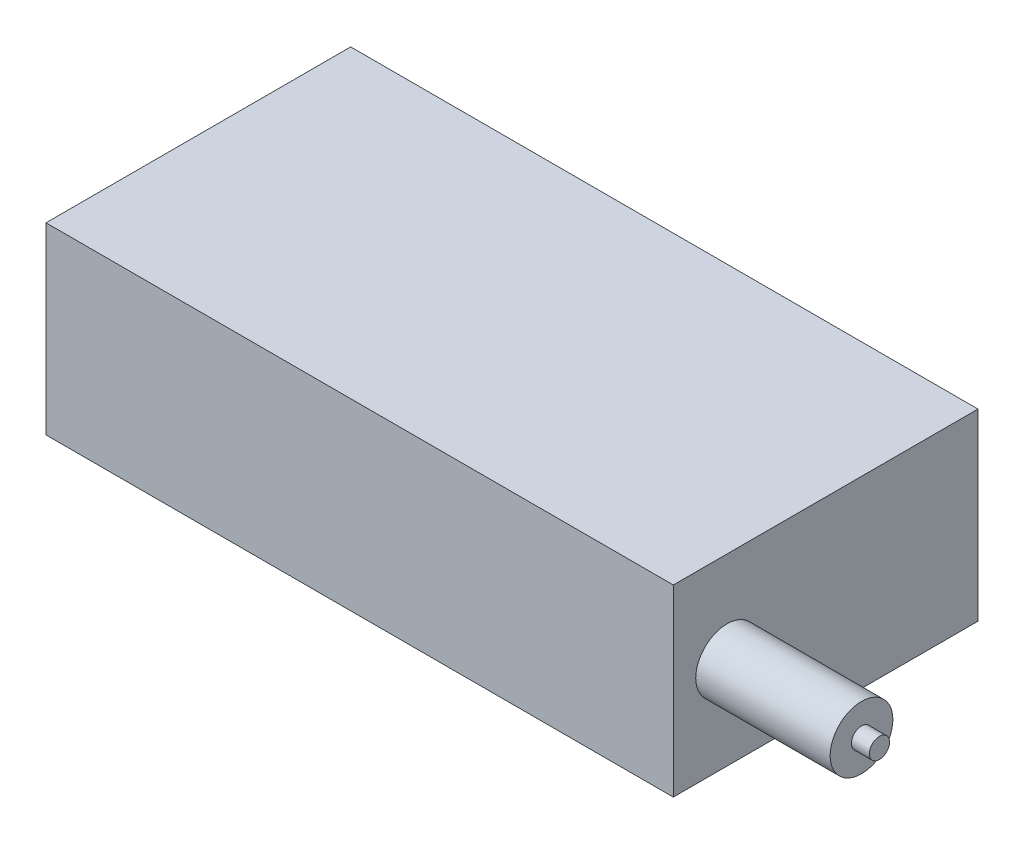
SolidWorks part; units mm, degrees
ref_plane "Front Plane" through (0, 0, 0) normal (0, 0, 1) x (1, 0, 0)
ref_plane "Top Plane" through (0, 0, 0) normal (0, 1, 0) x (1, 0, 0)
ref_plane "Right Plane" through (0, 0, 0) normal (1, 0, 0) x (0, 0, -1)
sketch "Sketch1" plane through (0, 0, 0) normal (0, 1, 0) x (1, 0, 0)
  line L1 (0, 0) -> (111.125, 0)
  line L2 (0, 0) -> (0, 53.975)
  line L3 (0, 53.975) -> (111.125, 53.975)
  line L4 (111.125, 0) -> (111.125, 53.975)
  dimension "D1" = 111.125
  dimension "D2" = 53.975
extrude "Boss-Extrude1" add sketch "Sketch1" along normal blind 32.5437
sketch "Sketch2" plane through (0, 0, 0) normal (-1, 0, 0) x (0, 0, 1)
  line L1 (-18.2562, 6.35) -> (-46.0375, 6.35)
  line L2 (-18.2562, 6.35) -> (-18.2562, 25.4)
  line L3 (-18.2562, 25.4) -> (-46.0375, 25.4)
  line L4 (-46.0375, 6.35) -> (-46.0375, 25.4)
  line L9 (-53.975, 0) -> (0, 0) construction
  line L10 (-53.975, 32.5437) -> (-53.975, 0) construction
  line L12 (-53.975, 0) -> (-46.0375, 0) construction
  line L13 (-53.975, 0) -> (-53.975, 6.35) construction
  line L14 (-53.975, 6.35) -> (-46.0375, 6.35) construction
  line L15 (-46.0375, 0) -> (-46.0375, 6.35) construction
  dimension "D1" = 27.7812
  dimension "D2" = 19.05
  dimension "D3" = 7.9375
  dimension "D4" = 6.35
extrude "Cut-Extrude1" cut sketch "Sketch2" against normal blind 3.175
sketch "Sketch4" plane through (111.125, 0, 0) normal (1, 0, 0) x (0, 0, -1)
  line L0 (0, 32.5437) -> (0, 0) construction
  line L1 (0, 0) -> (9.525, 0) construction
  line L2 (0, 0) -> (0, 16.2719) construction
  line L3 (0, 16.2719) -> (9.525, 16.2719) construction
  line L4 (9.525, 0) -> (9.525, 16.2719) construction
  circle A0 centre (9.525, 16.2719) radius 5.5562
  point P8 (0, 16.2719)
  dimension "D1" = 11.1125
  dimension "D2" = 9.525
extrude "Boss-Extrude2" add sketch "Sketch4" along normal blind 23.8125
sketch "Sketch5" plane through (134.9375, 0, 0) normal (1, 0, 0) x (0, 0, -1)
  circle A0 centre (9.525, 16.2719) radius 1.7859
  circle A1 centre (9.525, 16.2719) radius 5.5562 construction
  dimension "D1" = 3.5719
extrude "Boss-Extrude3" add sketch "Sketch5" along normal blind 3.175
